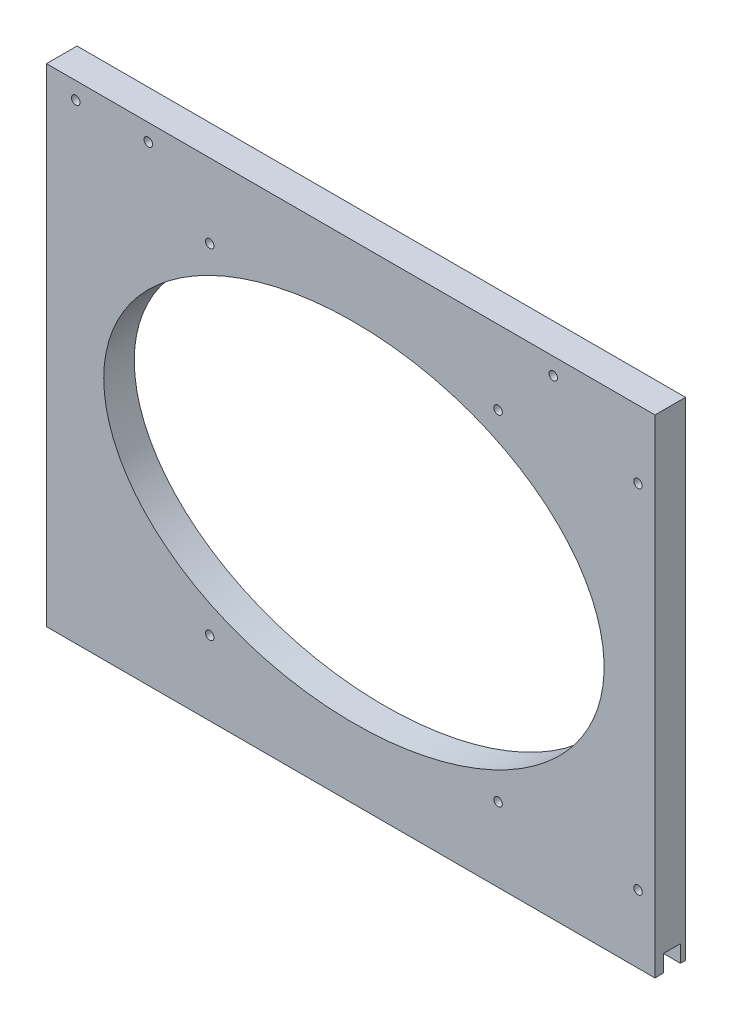
SolidWorks part; units mm, degrees
material "Pine"
ref_plane "Front Plane" through (0, 0, 0) normal (0, 0, 1) x (1, 0, 0)
ref_plane "Top Plane" through (0, 0, 0) normal (0, 1, 0) x (1, 0, 0)
ref_plane "Right Plane" through (0, 0, 0) normal (1, 0, 0) x (0, 0, -1)
sketch "Sketch1" plane through (0, 0, 0) normal (0, 0, 1) x (1, 0, 0)
  line L0 (-5300.6625, 1520.825) -> (-5451.475, 1520.825)
  line L1 (-5456.2375, 1384.3) -> (-5456.2375, 1516.0625)
  line L2 (-5557.8375, 1546.225) -> (-5194.3, 1546.225)
  line L3 (-5557.8375, 1539.875) -> (-5194.3, 1539.875)
  line L4 (-5297.4875, 1377.95) -> (-5454.65, 1377.95)
  line L5 (-5291.1375, 1384.3) -> (-5291.1375, 1516.0625)
  line L6 (-5300.6625, 1525.5875) -> (-5451.475, 1525.5875)
  line L7 (-5461, 1384.3) -> (-5461, 1516.0625)
  line L8 (-5297.4875, 1382.7125) -> (-5454.65, 1382.7125)
  line L9 (-5295.9, 1384.3) -> (-5295.9, 1516.0625)
  line L10 (-5740.4, 998.5375) -> (-5740.4, 1181.1)
  line L11 (-5740.4, 1181.1) -> (-5512.5938, 1181.1)
  line L12 (-5512.5938, 1181.1) -> (-5512.5938, 998.5375)
  line L13 (-5512.5938, 998.5375) -> (-5740.4, 998.5375)
  line L14 (-5258.5938, 1181.1) -> (-5486.4, 1181.1)
  line L15 (-5258.5938, 998.5375) -> (-5258.5938, 1181.1)
  line L16 (-5486.4, 998.5375) -> (-5258.5938, 998.5375)
  line L17 (-5486.4, 1181.1) -> (-5486.4, 998.5375)
  line L18 (-5740.4, 898.525) -> (-5011.7375, 898.525)
  line L19 (-5168.1062, 1384.3) -> (-5168.1062, 1392.2375)
  line L20 (-5176.0437, 1400.175) -> (-5245.8937, 1400.175)
  line L21 (-5253.8313, 1392.2375) -> (-5253.8313, 1384.3)
  line L22 (-5451.475, 1512.8875) -> (-5451.475, 1384.3)
  line L23 (-5303.8375, 1516.0625) -> (-5448.3, 1516.0625)
  line L24 (-5498.3062, 1384.3) -> (-5451.475, 1384.3)
  line L25 (-5253.8313, 1384.3) -> (-5300.6625, 1384.3)
  line L26 (-5584.0312, 1384.3) -> (-5740.4, 1384.3)
  line L27 (-5564.1875, 1536.7) -> (-5740.4, 1536.7)
  line L28 (-5740.4, 1357.3125) -> (-5740.4, 1206.5)
  line L29 (-5011.7375, 1357.3125) -> (-5740.4, 1357.3125)
  line L30 (-5011.7375, 1206.5) -> (-5011.7375, 1357.3125)
  line L31 (-5740.4, 1206.5) -> (-5011.7375, 1206.5)
  line L32 (-4765.675, 1549.4) -> (-4978.4, 1549.4)
  line L33 (-4765.675, 1397) -> (-4765.675, 1549.4)
  line L34 (-4978.4, 1397) -> (-4765.675, 1397)
  line L35 (-4978.4, 1549.4) -> (-4978.4, 1397)
  line L36 (-4765.675, 1371.6) -> (-4978.4, 1371.6)
  line L37 (-4765.675, 1219.2) -> (-4765.675, 1371.6)
  line L38 (-4978.4, 1219.2) -> (-4765.675, 1219.2)
  line L39 (-4978.4, 1371.6) -> (-4978.4, 1219.2)
  line L40 (-5284.7875, 803.275) -> (-5272.0875, 803.275)
  line L41 (-5187.95, 1536.7) -> (-5011.7375, 1536.7)
  line L42 (-5300.6625, 1384.3) -> (-5300.6625, 1512.8875)
  line L43 (-5740.4, 1536.7) -> (-5740.4, 1384.3)
  line L44 (-5557.8375, 1536.7) -> (-5557.8375, 1549.4)
  line L45 (-5557.8375, 1549.4) -> (-5194.3, 1549.4)
  line L46 (-5194.3, 1549.4) -> (-5194.3, 1536.7)
  line L47 (-5011.7375, 1536.7) -> (-5011.7375, 1384.3)
  line L48 (-5011.7375, 1384.3) -> (-5168.1062, 1384.3)
  line L49 (-5498.3062, 1384.3) -> (-5498.3062, 1392.2375)
  line L50 (-5506.2437, 1400.175) -> (-5576.0938, 1400.175)
  line L51 (-5584.0312, 1392.2375) -> (-5584.0312, 1384.3)
  line L52 (-5740.4, 660.4) -> (-5740.4, 898.525)
  line L53 (-5011.7375, 898.525) -> (-5011.7375, 660.4)
  line L54 (-5011.7375, 660.4) -> (-5740.4, 660.4)
  line L55 (-5291.1375, 803.275) -> (-5291.1375, 752.475)
  line L56 (-5265.7375, 752.475) -> (-5265.7375, 803.275)
  line L57 (-5284.7875, 752.475) -> (-5272.0875, 752.475)
  arc A0 (-5451.475, 1520.825) -> (-5456.2375, 1516.0625) centre (-5451.475, 1516.0625) ccw
  arc A1 (-5461, 1384.3) -> (-5454.65, 1377.95) centre (-5454.65, 1384.3) ccw
  arc A2 (-5297.4875, 1377.95) -> (-5291.1375, 1384.3) centre (-5297.4875, 1384.3) ccw
  circle A3 centre (-5037.9312, 1233.4875) radius 1.5875
  circle A4 centre (-5037.9312, 1328.7375) radius 1.5875
  circle A5 centre (-5714.2063, 1233.4875) radius 1.5875
  circle A6 centre (-5714.2063, 1328.7375) radius 1.5875
  circle A7 centre (-5018.0875, 1333.5) radius 1.5875
  circle A8 centre (-5018.0875, 1231.9) radius 1.5875
  circle A9 centre (-5734.05, 1231.9) radius 1.5875
  circle A10 centre (-5734.05, 1333.5) radius 1.5875
  circle A11 centre (-5734.05, 1511.3) radius 1.5875
  circle A12 centre (-5734.05, 1409.7) radius 1.5875
  circle A13 centre (-5018.0875, 1511.3) radius 1.5875
  circle A14 centre (-5018.0875, 1409.7) radius 1.5875
  arc A15 (-5557.8375, 1546.225) -> (-5557.8375, 1539.875) centre (-5557.8375, 1543.05) ccw
  arc A16 (-5194.3, 1539.875) -> (-5194.3, 1546.225) centre (-5194.3, 1543.05) ccw
  arc A17 (-5291.1375, 1516.0625) -> (-5300.6625, 1525.5875) centre (-5300.6625, 1516.0625) ccw
  arc A18 (-5451.475, 1525.5875) -> (-5461, 1516.0625) centre (-5451.475, 1516.0625) ccw
  arc A19 (-5456.2375, 1384.3) -> (-5454.65, 1382.7125) centre (-5454.65, 1384.3) ccw
  arc A20 (-5297.4875, 1382.7125) -> (-5295.9, 1384.3) centre (-5297.4875, 1384.3) ccw
  arc A21 (-5295.9, 1516.0625) -> (-5300.6625, 1520.825) centre (-5300.6625, 1516.0625) ccw
  circle A22 centre (-5702.3, 892.175) radius 1.5875
  circle A23 centre (-5734.05, 860.425) radius 1.5875
  circle A24 centre (-5474.8906, 892.175) radius 1.5875
  circle A25 centre (-5277.2469, 892.175) radius 1.5875
  circle A26 centre (-5049.8375, 892.175) radius 1.5875
  circle A27 centre (-5018.0875, 860.425) radius 1.5875
  circle A28 centre (-5296.6938, 1174.75) radius 1.5875
  circle A29 centre (-5448.3, 1174.75) radius 1.5875
  circle A30 centre (-5264.9437, 1155.7) radius 1.5875
  circle A31 centre (-5264.9437, 1023.9375) radius 1.5875
  circle A32 centre (-5518.9438, 1155.7) radius 1.5875
  circle A33 centre (-5518.9438, 1023.9375) radius 1.5875
  circle A34 centre (-5702.3, 1004.8875) radius 1.5875
  circle A35 centre (-5550.6937, 1004.8875) radius 1.5875
  arc A36 (-5576.0938, 1400.175) -> (-5584.0312, 1392.2375) centre (-5576.0938, 1392.2375) ccw
  arc A37 (-5168.1062, 1392.2375) -> (-5176.0437, 1400.175) centre (-5176.0437, 1392.2375) ccw
  arc A38 (-5245.8937, 1400.175) -> (-5253.8313, 1392.2375) centre (-5245.8937, 1392.2375) ccw
  arc A39 (-5448.3, 1516.0625) -> (-5451.475, 1512.8875) centre (-5448.3, 1512.8875) ccw
  arc A40 (-5284.7875, 803.275) -> (-5291.1375, 803.275) centre (-5287.9625, 803.275) ccw
  circle A41 centre (-5679.2812, 1026.3187) radius 1.5875
  circle A42 centre (-5679.2812, 1153.3187) radius 1.5875
  circle A43 centre (-5571.3313, 1153.3187) radius 1.5875
  circle A44 centre (-5571.3313, 1026.3187) radius 1.5875
  circle A45 centre (-5317.3312, 1153.3187) radius 1.5875
  circle A46 centre (-5317.3312, 1026.3187) radius 1.5875
  circle A47 centre (-5425.2812, 1026.3187) radius 1.5875
  circle A48 centre (-5425.2812, 1153.3187) radius 1.5875
  arc A49 (-5194.3, 1536.7) -> (-5187.95, 1536.7) centre (-5191.125, 1536.7) ccw
  arc A50 (-5564.1875, 1536.7) -> (-5557.8375, 1536.7) centre (-5561.0125, 1536.7) ccw
  arc A51 (-5300.6625, 1512.8875) -> (-5303.8375, 1516.0625) centre (-5303.8375, 1512.8875) ccw
  arc A52 (-5498.3062, 1392.2375) -> (-5506.2437, 1400.175) centre (-5506.2437, 1392.2375) ccw
  circle A53 centre (-5712.46, 784.225) radius 4.7625
  arc A54 (-5272.0875, 752.475) -> (-5265.7375, 752.475) centre (-5268.9125, 752.475) ccw
  arc A55 (-5291.1375, 752.475) -> (-5284.7875, 752.475) centre (-5287.9625, 752.475) ccw
  circle A56 centre (-5182.3938, 684.2125) radius 3.175
  circle A57 centre (-5239.5437, 684.2125) radius 3.175
  circle A58 centre (-5512.5938, 684.2125) radius 3.175
  circle A59 centre (-5569.7437, 684.2125) radius 3.175
  circle A60 centre (-5474.8906, 666.75) radius 1.5875
  circle A61 centre (-5277.2469, 666.75) radius 1.5875
  circle A62 centre (-5734.05, 698.5) radius 1.5875
  circle A63 centre (-5702.3, 666.75) radius 1.5875
  circle A64 centre (-5049.8375, 666.75) radius 1.5875
  circle A65 centre (-5018.0875, 698.5) radius 1.5875
  circle A66 centre (-5713.73, 835.025) radius 4.7625
  circle A67 centre (-5712.46, 819.785) radius 4.7625
  circle A68 centre (-5712.46, 802.005) radius 4.7625
  circle A69 centre (-5714.2063, 1314.45) radius 3.175
  circle A70 centre (-5037.9312, 1314.45) radius 3.175
  arc A71 (-5265.7375, 803.275) -> (-5272.0875, 803.275) centre (-5268.9125, 803.275) ccw
  ellipse E0 centre (-5371.3062, 1089.8188) end of major axis (-5277.6438, 1089.8188) minor radius 65.0875
  ellipse E1 centre (-5625.3062, 1089.8188) end of major axis (-5531.6438, 1089.8188) minor radius 65.0875
sketch "SpeakerPanel" plane through (0, 0, 0) normal (0, 0, 1) x (1, 0, 0)
  line L0 (-5258.5938, 1181.1) -> (-5258.5938, 998.5375)
  line L1 (-5258.5938, 998.5375) -> (-5486.4, 998.5375)
  line L2 (-5486.4, 998.5375) -> (-5486.4, 1181.1)
  line L3 (-5486.4, 1181.1) -> (-5258.5938, 1181.1)
  line L4 (-5372.4969, 1181.1) -> (-5372.4969, 998.5375) construction
  line L5 (-5372.4969, 1089.8188) -> (-5486.4, 1089.8188) construction
  line L6 (-5372.4969, 1089.8188) -> (-5258.5938, 1089.8188) construction
  dimension "D1" = 182.5625
  dimension "D2" = 227.8062
extrude "SpeakerPanel_Thickness" add sketch "SpeakerPanel" against normal blind 11.43
sketch "Sketch3" plane through (0, 0, 0) normal (0, 0, 1) x (1, 0, 0)
  line L0 (-5464.9688, 1089.8188) -> (-5277.6438, 1089.8188) construction
  line L1 (-5371.3062, 1154.9062) -> (-5371.3062, 1024.7313) construction
  circle A0 centre (-5448.3, 1174.75) radius 1.5875
  circle A1 centre (-5425.2812, 1153.3187) radius 1.5875
  circle A2 centre (-5296.6938, 1174.75) radius 1.5875
  circle A3 centre (-5317.3312, 1153.3187) radius 1.5875
  circle A4 centre (-5264.9437, 1155.7) radius 1.5875
  circle A5 centre (-5264.9437, 1023.9375) radius 1.5875
  circle A6 centre (-5317.3312, 1026.3187) radius 1.5875
  circle A7 centre (-5425.2812, 1026.3187) radius 1.5875
  ellipse E0 centre (-5371.3062, 1089.8188) end of major axis (-5464.9688, 1089.8188) minor radius 65.0875
extrude "SpeakerCutout" cut sketch "Sketch3" against normal up to surface (11.43 mm away) up to face at (-5372.4969, 1089.8188, -11.43)
sketch "Sketch4" plane through (-5258.5938, 0, 0) normal (1, 0, 0) x (0, 0, -1)
  line L0 (5.715, 998.5375) -> (3.175, 998.5375)
  line L1 (11.43, 998.5375) -> (0, 998.5375) construction
  line L2 (3.175, 998.5375) -> (3.175, 1004.8875)
  line L3 (3.175, 1004.8875) -> (9.525, 1004.8875)
  line L4 (9.525, 1004.8875) -> (9.525, 998.5375)
  line L5 (9.525, 998.5375) -> (5.715, 998.5375)
extrude "SpeakerSlotScreen" cut sketch "Sketch4" against normal up to surface (227.8062 mm away) up to face at (-5486.4, 1089.8188, -5.715)
sketch "Sketch5" plane through (0, 0, -11.43) normal (0, 0, -1) x (-1, 0, 0)
  circle A0 centre (5475.4335, 1174.75) radius 1.5875
extrude "Cut-Extrude1" cut sketch "Sketch5" against normal up to surface (11.43 mm away) up to face at (-5423.6937, 1026.3187, 0)
